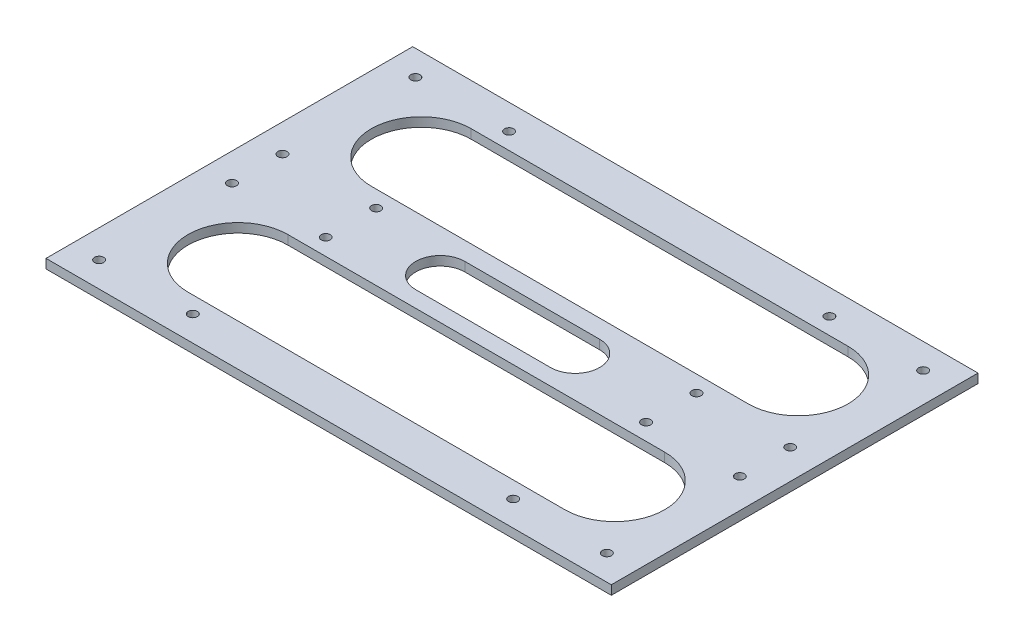
SolidWorks part; units mm, degrees
ref_plane "前视基准面" through (0, 0, 0) normal (0, 0, 1) x (1, 0, 0)
ref_plane "上视基准面" through (0, 0, 0) normal (0, 1, 0) x (1, 0, 0)
ref_plane "右视基准面" through (0, 0, 0) normal (1, 0, 0) x (0, 0, -1)
sketch "Sketch1" plane through (0, 0, 0) normal (0, 1, 0) x (1, 0, 0)
  line L1 (-172.7808, -58.8493) -> (12.2192, -58.8493)
  line L2 (-172.7808, -58.8493) -> (-172.7808, 1.1507)
  line L3 (-172.7808, 1.1507) -> (12.2192, 1.1507)
  line L4 (12.2192, -58.8493) -> (12.2192, 1.1507)
  line L5 (-172.7808, -58.8493) -> (12.2192, 1.1507) construction
  line L6 (-172.7808, 1.1507) -> (12.2192, -58.8493) construction
  point P0 (-80.2808, -28.8493)
  dimension "D1" = 60
  dimension "185" = 185
extrude "Boss-Extrude1" add sketch "Sketch1" along normal blind 3
sketch "Sketch2" plane through (0, 3, 0) normal (0, 1, 0) x (1, 0, 0)
  line L0 (-172.7808, -28.8493) -> (-162.1477, -28.8493) construction
  line L1 (-163.6533, -7.0993) -> (-28.1533, -7.0993) construction
  line L2 (-163.6533, -7.0993) -> (-163.6533, -50.5993) construction
  line L3 (-163.6533, -50.5993) -> (-28.1533, -50.5993) construction
  line L4 (-28.1533, -7.0993) -> (-28.1533, -50.5993) construction
  line L5 (-163.6533, -7.0993) -> (-28.1533, -50.5993) construction
  line L6 (-163.6533, -50.5993) -> (-28.1533, -7.0993) construction
  line L8 (-132.9861, -7.0993) -> (2.5139, -7.0993) construction
  line L9 (-132.9861, -7.0993) -> (-132.9861, -50.5993) construction
  line L10 (-132.9861, -50.5993) -> (2.5139, -50.5993) construction
  line L11 (2.5139, -7.0993) -> (2.5139, -50.5993) construction
  line L12 (-132.9861, -7.0993) -> (2.5139, -50.5993) construction
  line L13 (-132.9861, -50.5993) -> (2.5139, -7.0993) construction
  line L14 (-139.9762, -28.8493) -> (-16.6433, -28.8493) construction
  line L15 (-139.9762, -12.5158) -> (-16.6433, -12.5158)
  line L16 (-139.9762, -45.1829) -> (-16.6433, -45.1829)
  circle A0 centre (-163.6533, -7.0993) radius 1.5
  circle A1 centre (-163.6533, -50.5993) radius 1.5
  circle A2 centre (-28.1533, -50.5993) radius 1.5
  circle A3 centre (-28.1533, -7.0993) radius 1.5
  circle A4 centre (-132.9861, -7.0993) radius 1.5
  circle A5 centre (-132.9861, -50.5993) radius 1.5
  circle A6 centre (2.5139, -50.5993) radius 1.5
  circle A7 centre (2.5139, -7.0993) radius 1.5
  arc A8 (-139.9762, -12.5158) -> (-139.9762, -45.1829) centre (-139.9762, -28.8493) ccw
  arc A9 (-16.6433, -45.1829) -> (-16.6433, -12.5158) centre (-16.6433, -28.8493) ccw
  point P0 (-95.9033, -28.8493)
  point P10 (-78.3097, -28.8493)
  point P12 (-65.2361, -28.8493)
  dimension "D3" = 135.5
  dimension "D1" = 135.5
  dimension "D2" = 43.5
extrude "Cut-Extrude1" cut sketch "Sketch2" against normal blind 3
mirror "Mirror1" about plane through (-172.7808, 3, 58.8493) normal (0, 0, -1) of bodies 107
sketch "Sketch3" plane through (0, 3, 0) normal (0, 1, 0) x (1, 0, 0)
  line L0 (-172.7808, -59.2009) -> (-163.6444, -59.2009) construction
  line L2 (-103.405, -59.2009) -> (-59.281, -59.2009) construction
  line L3 (-103.405, -53.2371) -> (-59.281, -53.2371) construction
  line L4 (-103.405, -53.2371) -> (-103.405, -65.1647) construction
  line L5 (-103.405, -65.1647) -> (-59.281, -65.1647) construction
  line L6 (-59.281, -53.2371) -> (-59.281, -65.1647) construction
  line L7 (-103.405, -53.2371) -> (-59.281, -65.1647) construction
  line L8 (-103.405, -65.1647) -> (-59.281, -53.2371) construction
  line L9 (-103.405, -51.1736) -> (-59.281, -51.1736)
  line L10 (-103.405, -67.2282) -> (-59.281, -67.2282)
  arc A0 (-103.405, -51.1736) -> (-103.405, -67.2282) centre (-103.405, -59.2009) ccw
  arc A1 (-59.281, -67.2282) -> (-59.281, -51.1736) centre (-59.281, -59.2009) ccw
  point P1 (-81.343, -59.2009)
  point P9 (-81.343, -59.2009)
  point P14 (0, 0)
  point P15 (-81.343, -59.2009)
extrude "Cut-Extrude2" cut sketch "Sketch3" against normal blind 10
